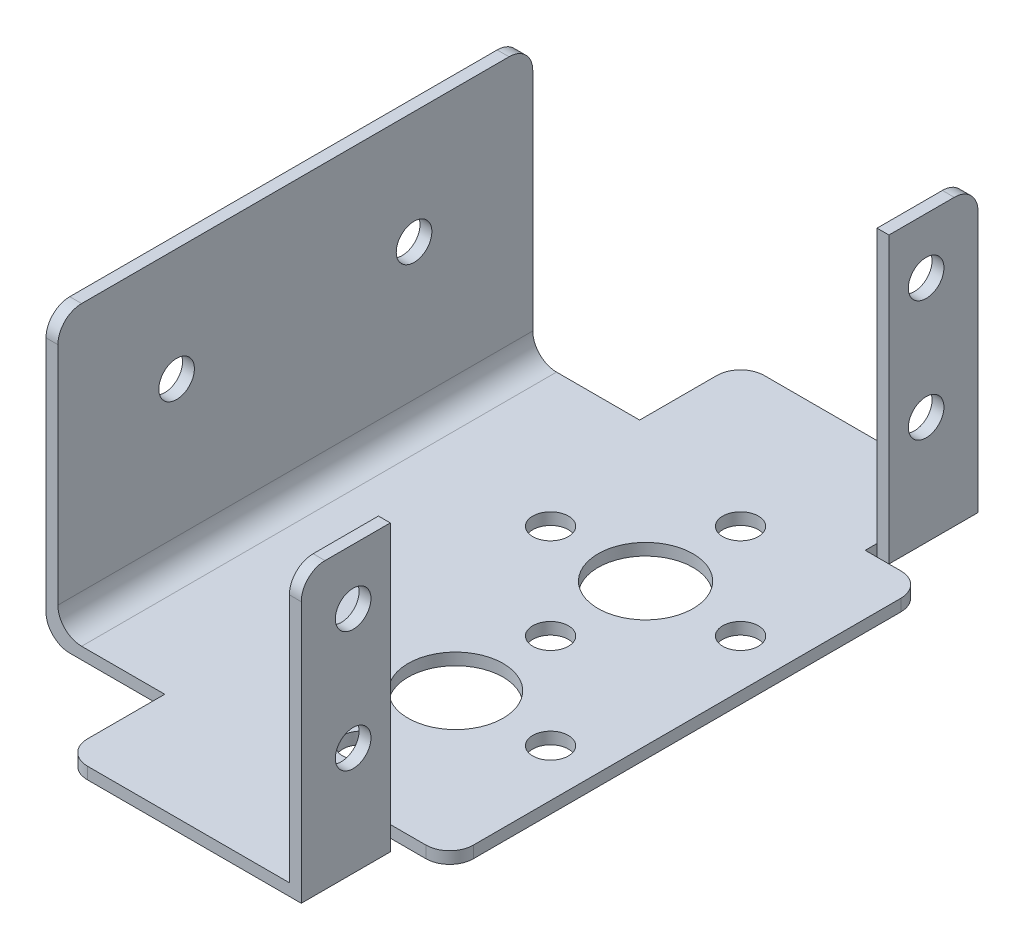
SolidWorks part; units mm, degrees
material "Plain Carbon Steel"
ref_plane "Front Plane" through (0, 0, 0) normal (0, 0, 1) x (1, 0, 0)
ref_plane "Top Plane" through (0, 0, 0) normal (0, 1, 0) x (1, 0, 0)
ref_plane "Right Plane" through (0, 0, 0) normal (1, 0, 0) x (0, 0, -1)
sketch "Sketch1" plane through (0, 0, 0) normal (0, 0, 1) x (1, 0, 0)
  line L0 (-46.6929, 15.875) -> (-46.6929, -8.125)
  line L1 (-46.6929, -8.125) -> (-16.6929, -8.125)
  line L2 (-16.6929, -8.125) -> (-16.6929, 15.875)
  line L3 (-45.6929, 15.875) -> (-45.6929, -7.125)
  line L4 (-45.6929, -7.125) -> (-17.6929, -7.125)
  line L5 (-17.6929, -7.125) -> (-17.6929, 15.875)
  line L6 (-46.6929, 15.875) -> (-45.6929, 15.875)
  line L7 (-17.6929, 15.875) -> (-16.6929, 15.875)
  dimension "D3" = 1
  dimension "D1" = 24
  dimension "D2" = 30
extrude "Boss-Extrude1" add sketch "Sketch1" along normal blind 57
sketch "Sketch2" plane through (-16.6929, 0, 0) normal (1, 0, 0) x (0, 0, -1)
  line L0 (-57, 15.875) -> (0, 15.875) construction
  line L1 (-49.5, 15.875) -> (-7.5, 15.875)
  line L2 (-49.5, 15.875) -> (-49.5, -8.125)
  line L3 (-49.5, -8.125) -> (-7.5, -8.125)
  line L4 (-7.5, 15.875) -> (-7.5, -8.125)
  line L5 (-57, -8.125) -> (0, -8.125) construction
  line L6 (-57, -8.125) -> (-57, 15.875) construction
  line L7 (0, -8.125) -> (0, 15.875) construction
  dimension "D1" = 7.5
  dimension "D2" = 7.5
extrude "Cut-Extrude1" cut sketch "Sketch2" against normal blind 1
sketch "Sketch3" plane through (-16.6929, 0, 0) normal (1, 0, 0) x (0, 0, -1)
  line L1 (-57, 15.875) -> (-49.5, 15.875) construction
  line L2 (-57, -8.125) -> (-57, 15.875) construction
  circle A0 centre (-52.63, 11.176) radius 1.5
  circle A1 centre (-4.37, 11.176) radius 1.5
  circle A2 centre (-4.37, 1.016) radius 1.5
  circle A3 centre (-52.63, 1.016) radius 1.5
  dimension "D1" = 4.37
  dimension "D5" = 10.16
  dimension "D6" = 48.26
  dimension "D2" = 4.699
  dimension "D3" = 2
  dimension "D4" = 2
extrude "Cut-Extrude2" cut sketch "Sketch3" against normal blind 2.54
sketch "Sketch4" plane through (-46.6929, 0, 0) normal (-1, 0, 0) x (0, 0, 1)
  line L0 (57, -8.125) -> (0, -8.125) construction
  line L1 (0, 15.875) -> (8.5, 15.875)
  line L2 (0, 15.875) -> (0, -8.125)
  line L3 (0, -8.125) -> (8.5, -8.125)
  line L4 (8.5, 15.875) -> (8.5, -8.125)
  line L6 (57, 15.875) -> (48.5, 15.875)
  line L7 (57, 15.875) -> (57, -8.125)
  line L8 (57, -8.125) -> (48.5, -8.125)
  line L9 (48.5, 15.875) -> (48.5, -8.125)
  dimension "D1" = 8.5
  dimension "D2" = 8.5
extrude "Cut-Extrude3" cut sketch "Sketch4" against normal blind 10
sketch "Sketch5" plane through (-46.6929, 0, 0) normal (-1, 0, 0) x (0, 0, 1)
  line L0 (48.5, 15.875) -> (48.5, -8.125) construction
  line L1 (48.5, 15.875) -> (8.5, 15.875) construction
  circle A0 centre (38.5, 6.375) radius 1.5
  circle A1 centre (18.5, 6.375) radius 1.5
  dimension "D1" = 10
  dimension "D2" = 9.5
  dimension "D3" = 2
extrude "Cut-Extrude4" cut sketch "Sketch5" against normal blind 10
sketch "Sketch6" plane through (-17.6929, 0, 0) normal (1, 0, 0) x (0, 0, -1)
  line L0 (-49.5, -8.125) -> (-7.5, -8.125) construction
  line L1 (-8.5, -7.125) -> (-48.5, -7.125)
  line L2 (-8.5, -7.125) -> (-8.5, -8.125)
  line L3 (-8.5, -8.125) -> (-48.5, -8.125)
  line L4 (-48.5, -7.125) -> (-48.5, -8.125)
extrude "Boss-Extrude2" add sketch "Sketch6" along normal blind 5
sketch "Sketch7" plane through (0, -8.125, 0) normal (0, -1, 0) x (-1, 0, 0)
  line L0 (36.6929, 0) -> (16.6929, 0) construction
  line L1 (12.6929, -48.5) -> (12.6929, -8.5) construction
  circle A0 centre (24.6929, -20) radius 4
  circle A1 centre (24.6929, -12) radius 1.5
  circle A2 centre (32.6929, -20) radius 1.5
  circle A3 centre (24.6929, -28) radius 1.5
  circle A4 centre (16.6929, -20) radius 1.5
  circle A5 centre (24.6929, -28) radius 1.5
  circle A6 centre (32.6929, -36) radius 1.5
  circle A7 centre (24.6929, -44) radius 1.5
  circle A8 centre (16.6929, -36) radius 1.5
  circle A9 centre (24.6929, -36) radius 4
  point P18 (24.6929, -20)
  dimension "D1" = 20
  dimension "D2" = 12
  dimension "D3" = 8
  dimension "D4" = 4
extrude "Cut-Extrude5" cut sketch "Sketch7" against normal blind 1 contours A2 | A0 | A4 | A1 | A6 | A9 | A8 | A3 | A7
fillet "Fillet1" radius 2 10 edges at (-12.6929, -7.625, 48.5) (-12.6929, -7.625, 8.5) (-36.6929, -7.625, 0) (-36.6929, -7.625, 57) (-46.1929, 15.875, 48.5) (-46.1929, 15.875, 8.5) (-17.1929, 15.875, 0) (-17.1929, 15.875, 57) (-46.6929, -8.125, 28.5) (-45.6929, -7.125, 28.5)
